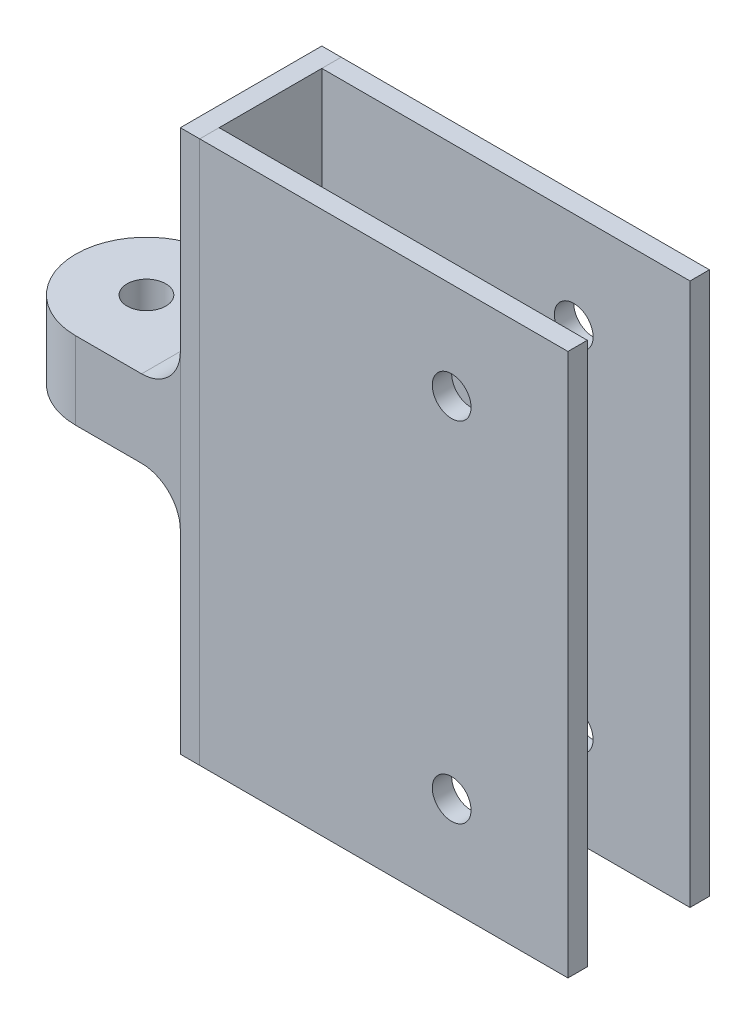
SolidWorks part; units mm, degrees
other "Pulley Mount"
material "AISI 1020"
ref_plane "Front Plane" through (0, 0, 0) normal (0, 0, 1) x (1, 0, 0)
ref_plane "Top Plane" through (0, 0, 0) normal (0, 1, 0) x (1, 0, 0)
ref_plane "Right Plane" through (0, 0, 0) normal (1, 0, 0) x (0, 0, -1)
sketch "Sketch1" plane through (0, 0, 0) normal (0, 1, 0) x (1, 0, 0)
  line L0 (5, 18.25) -> (-27, 18.25) construction
  line L1 (0, 0) -> (100, 0)
  line L2 (0, 0) -> (0, 5)
  line L3 (0, 5) -> (100, 5)
  line L4 (100, 0) -> (100, 5)
  line L5 (0, 0) -> (5, 0)
  line L6 (0, 0) -> (0, 36.5)
  line L7 (0, 36.5) -> (5, 36.5)
  line L8 (5, 0) -> (5, 36.5)
  line L9 (0, 36.5) -> (100, 36.5)
  line L10 (0, 36.5) -> (0, 31.5)
  line L11 (0, 31.5) -> (100, 31.5)
  line L12 (100, 36.5) -> (100, 31.5)
  line L15 (-27, 36.5) -> (0, 36.5)
  line L16 (-27, 0) -> (0, 0)
  arc A1 (-27, 36.5) -> (-27, 0) centre (-27, 18.25) ccw
  dimension "D8" = 27
  dimension "D1" = 5
  dimension "D3" = 26.5
  dimension "D4" = 5
  dimension "D6" = 100
extrude "Boss-Extrude1" add sketch "Sketch1" along normal blind 20
sketch "Sketch2" plane through (0, 20, 0) normal (0, 1, 0) x (1, 0, 0)
  line L37 (100, 0) -> (0, 0)
  line L38 (100, 0) -> (100, 1.6827)
  line L39 (100, 1.6827) -> (0, 1.6827)
  line L40 (0, 0) -> (0, 1.6827)
  line L46 (-27, 36.5) -> (100, 36.5) construction
  line L47 (0, 1.6827) -> (5, 1.6827)
  line L48 (0, 1.6827) -> (0, 36.5)
  line L49 (0, 36.5) -> (5, 36.5)
  line L50 (5, 1.6827) -> (5, 36.5)
  line L52 (5, 36.5) -> (100, 36.5)
  line L53 (5, 36.5) -> (5, 31.5)
  line L54 (5, 31.5) -> (100, 31.5)
  line L55 (100, 36.5) -> (100, 31.5)
  dimension "D2" = 100
  dimension "D3" = 5
  dimension "D4" = 5
  dimension "D5" = 95
extrude "Boss-Extrude2" add sketch "Sketch2" along normal blind 60
sketch "Sketch3" plane through (0, 0, 0) normal (0, -1, 0) x (1, 0, 0)
  line L0 (-27, 0) -> (100, 0) construction
  line L17 (100, -36.5) -> (0, -36.5)
  line L18 (100, -36.5) -> (100, -31.5)
  line L19 (100, -31.5) -> (0, -31.5)
  line L20 (0, -36.5) -> (0, -31.5)
  line L21 (0, -31.5) -> (6, -31.5)
  line L22 (0, -31.5) -> (0, 0)
  line L23 (0, 0) -> (6, 0)
  line L24 (6, -31.5) -> (6, 0)
  line L26 (6, 0) -> (100, 0)
  line L27 (6, 0) -> (6, -5)
  line L28 (6, -5) -> (100, -5)
  line L29 (100, 0) -> (100, -5)
  dimension "D1" = 5
  dimension "D2" = 100
  dimension "D3" = 6
  dimension "D4" = 94
  dimension "D5" = 5
extrude "Boss-Extrude3" add sketch "Sketch3" along normal blind 60
sketch "Sketch4" plane through (0, 0, 0) normal (0, 0, 1) x (1, 0, 0)
  line L1 (100, 80) -> (100, -60) construction
  line L3 (70, 55) -> (70, -35) construction
  line L4 (70, 10) -> (100, 10) construction
  dimension "D3" = 90
  dimension "D4" = 30
hole_wizard "M8 Clearance Hole1" positions "Sketch5" profile "Sketch7" hole size "M8" standard "ANSI Metric" end condition up to next
sketch "Sketch5" plane through (0, 20, 0) normal (0, 1, 0) x (1, 0, 0)
  point P0 (-27, 18.25)
sketch "Sketch7" plane through (-27, 20, -18.25) normal (1, 0, 0) x (0, 0, 1)
  line L0 (0, 0) -> (0, 20)
  line L1 (0, 20) -> (5, 20)
  line L2 (5, 20) -> (5, 0)
  line L5 (5, 0) -> (0, 0)
  line L11 (0, -6.35) -> (0, 107.95) construction
  dimension "Thru Hole Dia." = 10
  dimension "Thru Hole Depth" = 20
hole_wizard "M8 Clearance Hole2" positions "Sketch8" profile "Sketch9" hole size "M8" standard "ANSI Metric" end condition through all
sketch "Sketch8" plane through (0, 0, 0) normal (0, 0, 1) x (1, 0, 0)
  point P0 (70, 55)
  point P3 (70, -35)
sketch "Sketch9" plane through (70, 55, 0) normal (1, 0, 0) x (0, -1, 0)
  line L0 (0, 0) -> (0, 36.5)
  line L1 (0, 36.5) -> (5, 36.5)
  line L2 (5, 36.5) -> (5, 0)
  line L5 (5, 0) -> (0, 0)
  line L11 (0, -6.35) -> (0, 107.95) construction
  dimension "Thru Hole Dia." = 10
  dimension "Thru Hole Depth" = 36.5
fillet "Fillet2" radius 10 2 edges at (0, 0, -18.25) (0, 20, -18.25)
sketch "Sketch11" plane through (0, 0, 0) normal (0, 1, 0) x (1, 0, 0)
  line L0 (0, 36.5) -> (0, 0)
  line L1 (5, 5) -> (5, 0)
  line L2 (0, 0) -> (100, 0) construction
  line L3 (5, 31.5) -> (5, 36.5)
  line L4 (100, 36.5) -> (0, 36.5) construction
split "Split1" trim tools "Sketch11" bodies to split 115 resulting bodies 116 117 118 119
equation "\"f\"= 0.4'fuzzy skin offset"
